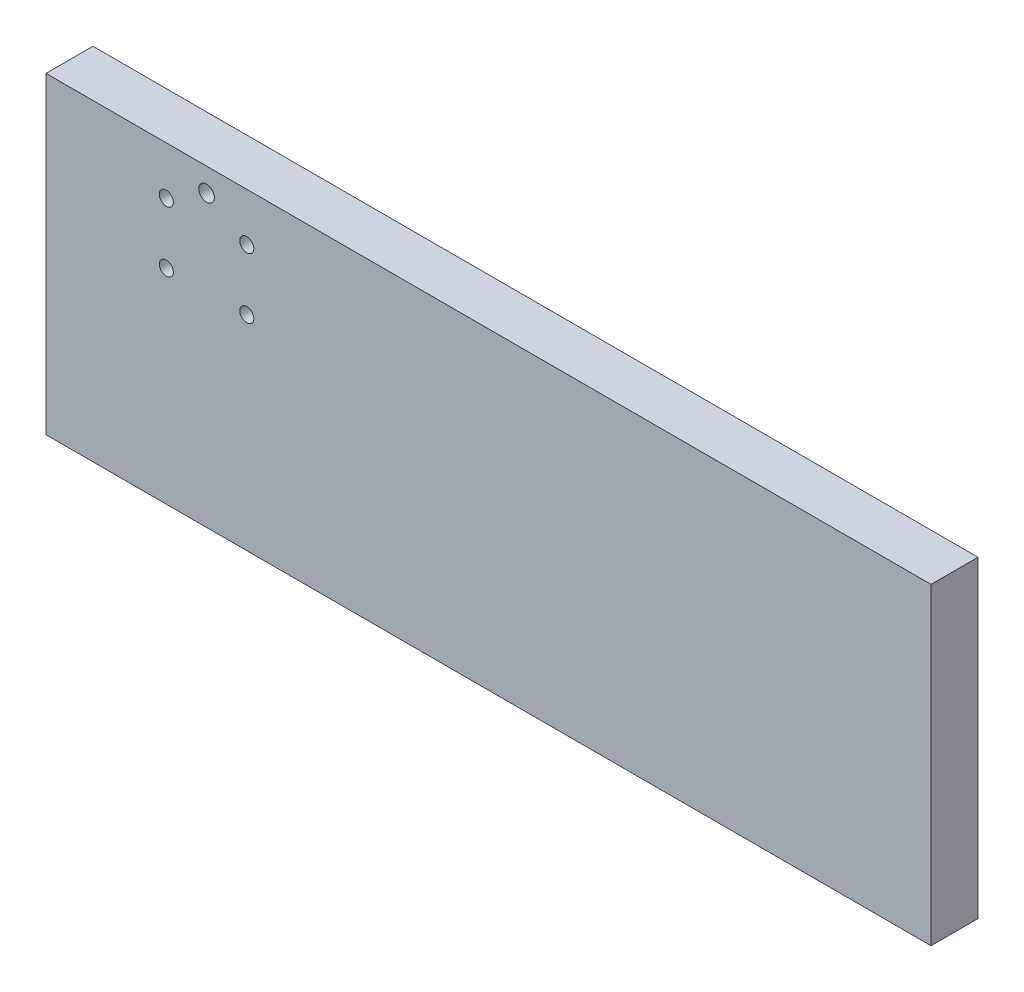
SolidWorks part; units mm, degrees
ref_plane "Front Plane" through (0, 0, 0) normal (0, 0, 1) x (1, 0, 0)
ref_plane "Top Plane" through (0, 0, 0) normal (0, 1, 0) x (1, 0, 0)
ref_plane "Right Plane" through (0, 0, 0) normal (1, 0, 0) x (0, 0, -1)
sketch "Sketch1" plane through (0, 0, 0) normal (0, 0, 1) x (1, 0, 0)
  line L1 (0, 0) -> (359.156, 0)
  line L2 (0, 0) -> (0, 127)
  line L3 (0, 127) -> (359.156, 127)
  line L4 (359.156, 0) -> (359.156, 127)
  dimension "D1" = 127
  dimension "D2" = 359.156
extrude "Boss-Extrude1" add sketch "Sketch1" along normal blind 19.05
sketch "Sketch2" plane through (0, 0, 19.05) normal (0, 0, 1) x (1, 0, 0)
  circle A0 centre (48.8251, 82.9627) radius 2.8511
  circle A1 centre (48.8251, 107.5372) radius 2.8511
  circle A2 centre (81.4768, 107.5372) radius 2.8512
  circle A3 centre (81.4768, 82.9627) radius 2.8512
extrude "Cut-Extrude1" cut sketch "Sketch2" against normal up to next
sketch "Sketch3" plane through (0, 0, 0) normal (0, 0, -1) x (-1, 0, 0)
  line L0 (-65.151, 114.3) -> (-65.151, 117.475) construction
  line L1 (-58.6607, 114.3) -> (-71.6413, 114.3) construction
  circle A1 centre (-65.151, 117.475) radius 3.175
  dimension "D1" = 3.175
  dimension "D2" = 6.35
extrude "Cut-Extrude2" cut sketch "Sketch3" against normal up to next
